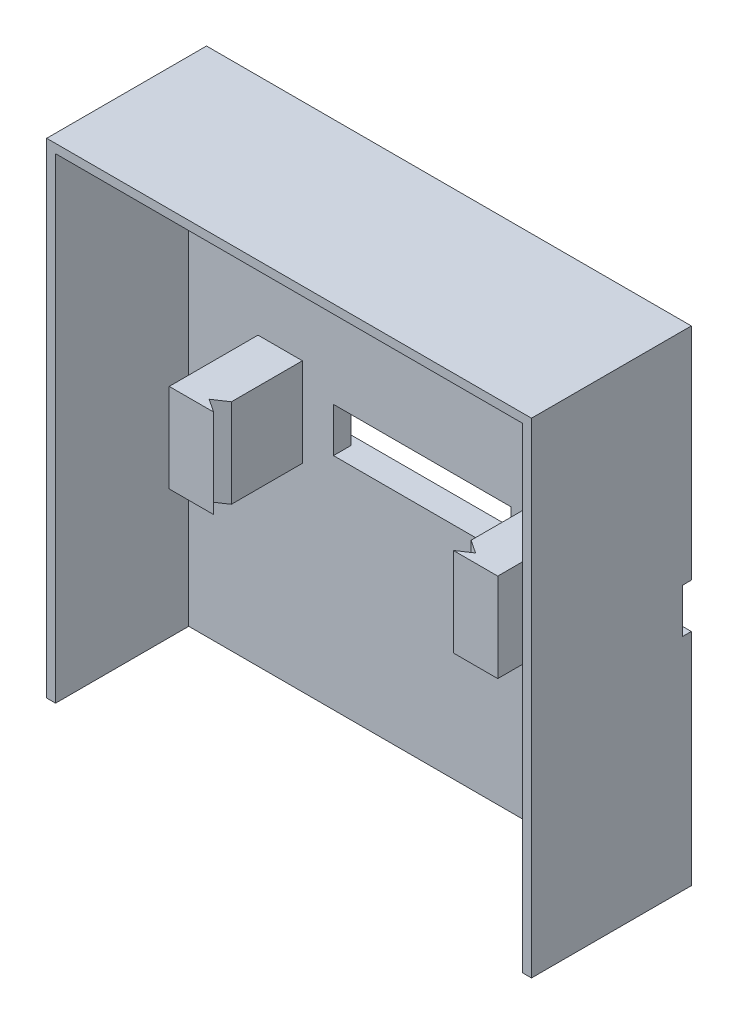
SolidWorks part; units mm, degrees
ref_plane "Přední rovina" through (0, 0, 0) normal (0, 0, 1) x (1, 0, 0)
ref_plane "Horní rovina" through (0, 0, 0) normal (0, 1, 0) x (1, 0, 0)
ref_plane "Pravá rovina" through (0, 0, 0) normal (1, 0, 0) x (0, 0, -1)
sketch "Skica1" plane through (0, 0, 0) normal (0, 0, 1) x (1, 0, 0)
  line L1 (27.3, 27.3) -> (-27.3, 27.3)
  line L2 (27.3, 27.3) -> (27.3, -27.3)
  line L3 (27.3, -27.3) -> (-27.3, -27.3)
  line L4 (-27.3, 27.3) -> (-27.3, -27.3)
  line L5 (27.3, 27.3) -> (-27.3, -27.3) construction
  line L6 (27.3, -27.3) -> (-27.3, 27.3) construction
  point P0 (0, 0)
  point P5 (-27.5, 0)
  point P11 (4.5, 0)
  dimension "D1" = 54.6
  dimension "D2" = 54.6
extrude "Přidat vysunutím2" add sketch "Skica1" along normal blind 3 contours L2 L1 L4 L3
sketch "Skica4" plane through (0, 0, 3) normal (0, 0, 1) x (1, 0, 0)
  line L1 (-10, 2.5) -> (10, 2.5)
  line L2 (-10, 2.5) -> (-10, -2.5)
  line L3 (-10, -2.5) -> (10, -2.5)
  line L4 (10, 2.5) -> (10, -2.5)
  line L5 (-10, 2.5) -> (10, -2.5) construction
  line L6 (-10, -2.5) -> (10, 2.5) construction
  line L10 (-27.3, 27.3) -> (-27.3, -27.3) construction
  point P0 (0, 0)
  point P7 (0, 0)
  point P10 (0, 0)
  point P11 (0, 0)
  point P12 (0, 0)
  point P13 (0, 0)
  dimension "D1" = 5
  dimension "D2" = 20
  dimension "D3" = 17.3
extrude "Odebrat vysunutím1" cut sketch "Skica4" against normal blind 2
sketch "Skica5" plane through (0, 0, 0) normal (0, 0, -1) x (-1, 0, 0)
  line L10 (27.3, 27.3) -> (27.3, -27.3) construction
  line L11 (-27.3, 2.5) -> (27.3, 2.5)
  line L12 (-27.3, 2.5) -> (-27.3, -2.5)
  line L13 (-27.3, -2.5) -> (27.3, -2.5)
  line L14 (27.3, 2.5) -> (27.3, -2.5)
  line L15 (-27.3, 2.5) -> (27.3, -2.5) construction
  line L16 (-27.3, -2.5) -> (27.3, 2.5) construction
  point P0 (0, 0)
  dimension "D1" = 5
extrude "Odebrat vysunutím3" cut sketch "Skica5" against normal blind 1 contours L11 L14 L13 L12
sketch "Skica10" plane through (0, 0, 3) normal (0, 0, 1) x (1, 0, 0)
  line L5 (-10, 2.5) -> (-10, -2.5) construction
  line L6 (-13.5, 5) -> (-18.5, 5)
  line L7 (13.5, 5) -> (18.5, 5)
  line L8 (13.5, 5) -> (13.5, -5)
  line L9 (13.5, -5) -> (18.5, -5)
  line L10 (18.5, 5) -> (18.5, -5)
  line L11 (13.5, 5) -> (18.5, -5) construction
  line L12 (13.5, -5) -> (18.5, 5) construction
  line L14 (-13.5, 5) -> (-13.5, -5)
  line L15 (-13.5, -5) -> (-18.5, -5)
  line L16 (-18.5, 5) -> (-18.5, -5)
  line L17 (-13.5, 5) -> (-18.5, -5) construction
  line L18 (-13.5, -5) -> (-18.5, 5) construction
  line L19 (10, -2.5) -> (10, 2.5) construction
  point P0 (-16, 0)
  point P5 (16, 0)
  point P10 (-13.5, 0)
  dimension "D1" = 10
  dimension "D2" = 5
  dimension "D3" = 5
  dimension "D4" = 27
  dimension "D5" = 10
  dimension "D6" = 3.5
  dimension "D7" = 3.5
  dimension "D8" = 0
extrude "Přidat vysunutím6" add sketch "Skica10" along normal blind 10
sketch "Skica12" plane through (0, 5, 0) normal (0, 1, 0) x (1, 0, 0)
  line L0 (-13.5, -13) -> (-13.5, -11)
  line L1 (-13.5, -13) -> (-13.5, -3) construction
  line L2 (-13.5, -11) -> (-15, -12)
  line L3 (-15, -12) -> (-13.5, -13)
  line L4 (13.5, -13) -> (13.5, -11)
  line L5 (13.5, -13) -> (13.5, -3) construction
  line L6 (13.5, -11) -> (15, -12)
  line L7 (15, -12) -> (13.5, -13)
  dimension "D2" = 1.5
  dimension "D1" = 2
  dimension "D3" = 1.5
extrude "Odebrat vysunutím6" cut sketch "Skica12" against normal blind 10
sketch "Skica14" plane through (0, 0, 3) normal (0, 0, 1) x (1, 0, 0)
  line L1 (-27.3, 27.3) -> (27.3, 27.3)
  line L2 (-27.3, 27.3) -> (-27.3, -27.3)
  line L3 (-27.3, -27.3) -> (27.3, -27.3)
  line L4 (27.3, 27.3) -> (27.3, -27.3)
  line L5 (-26.3, 26.3) -> (26.3, 26.3)
  line L6 (-26.3, 26.3) -> (-26.3, -27.3)
  line L7 (-26.3, -27.3) -> (26.3, -27.3)
  line L8 (26.3, 26.3) -> (26.3, -27.3)
  line M13 (-27.3, -27.3) -> (27.3, -27.3)
  line M14 (27.3, -27.3) -> (27.3, 27.3)
  line M15 (27.3, 27.3) -> (-27.3, 27.3)
  line M16 (-27.3, 27.3) -> (-27.3, -27.3)
  dimension "D1" = 1
  dimension "D2" = 1
  dimension "D3" = 1
  dimension "D4" = 0
extrude "Přidat vysunutím9" add sketch "Skica14" along normal blind 15 contours L5 L8 L6 M13 M14 M15 M16
sketch "Skica17" plane through (0, 0, 1) normal (0, 0, -1) x (-1, 0, 0)
  line L0 (-27.3, 2.5) -> (-27.3, -2.5) construction
  line L1 (-10, -2.5) -> (-10, 2.5) construction
  line L2 (27.3, 2.5) -> (27.3, -2.5) construction
  circle A0 centre (-18.3, 0) radius 2
  circle A1 centre (18.3, 0) radius 2
  dimension "D1" = 4
  dimension "D2" = 4
  dimension "D3" = 9
  dimension "D4" = 8.3
  dimension "D5" = 9
extrude "Odebrat vysunutím8" cut sketch "Skica17" against normal blind 4
